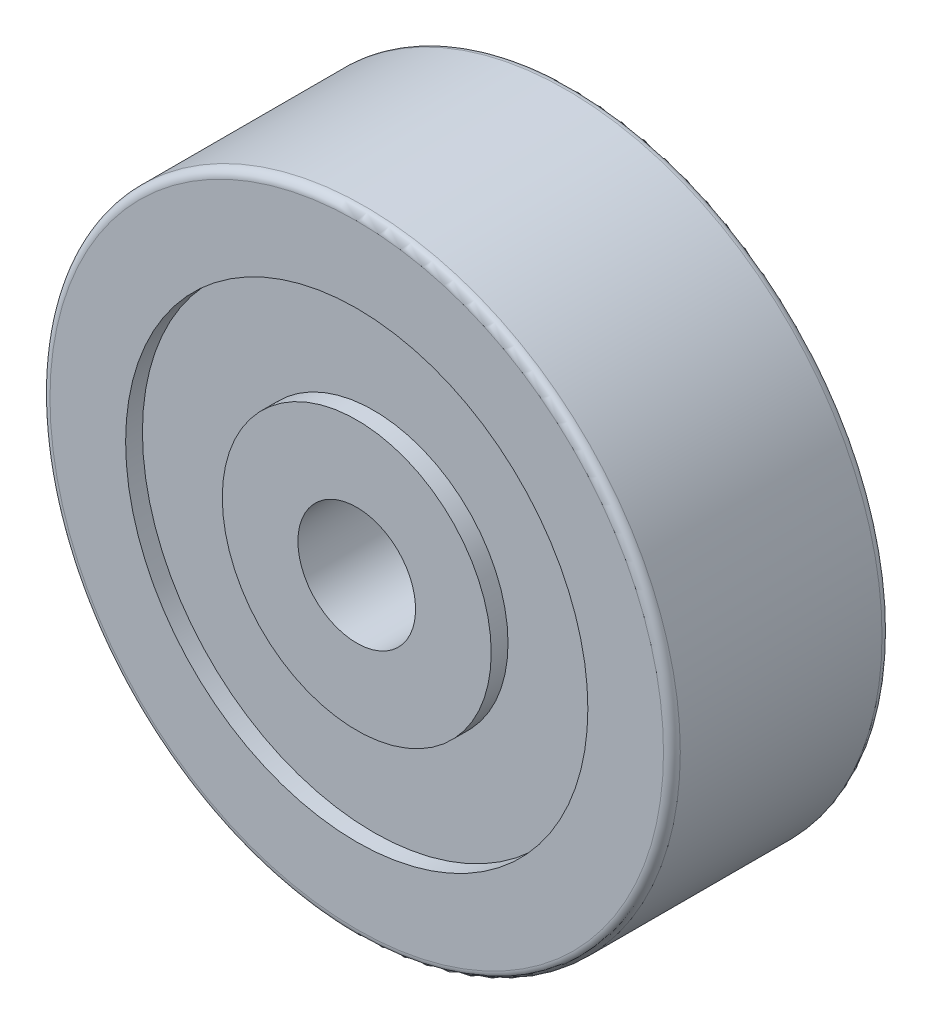
SolidWorks part; units mm, degrees
material "Alloy Steel"
ref_plane "Front Plane" through (0, 0, 0) normal (0, 0, 1) x (1, 0, 0)
ref_plane "Top Plane" through (0, 0, 0) normal (0, 1, 0) x (1, 0, 0)
ref_plane "Right Plane" through (0, 0, 0) normal (1, 0, 0) x (0, 0, -1)
sketch "Sketch1" plane through (0, 0, 0) normal (0, 0, 1) x (1, 0, 0)
  circle A0 centre (0, 0) radius 37.5
  dimension "D1" = 75
extrude "Boss-Extrude1" add sketch "Sketch1" against normal mid plane 26
ref_plane "Plane1" through (0, 0, 11) normal (0, 0, 1) x (1, 0, 0)
sketch "Sketch4" plane through (0, 0, -13) normal (0, 0, -1) x (-1, 0, 0)
  circle A0 centre (0, 0) radius 27.5
  dimension "D1" = 55
extrude "Cut-Extrude1" cut sketch "Sketch4" against normal blind 2
mirror "Mirror1" about plane through (0, 0, 0) normal (0, 0, 1) of "Cut-Extrude1"
sketch "Sketch5" plane through (0, 0, -11) normal (0, 0, -1) x (-1, 0, 0)
  circle A0 centre (0, 0) radius 16
  dimension "D1" = 32
extrude "Boss-Extrude2" add sketch "Sketch5" along normal blind 2
mirror "Mirror2" about plane through (0, 0, 0) normal (0, 0, 1) of "Boss-Extrude2"
sketch "Sketch6" plane through (0, 0, -13) normal (0, 0, -1) x (-1, 0, 0)
  circle A0 centre (0, 0) radius 7
  dimension "D1" = 14
extrude "Cut-Extrude2" cut sketch "Sketch6" against normal through all
fillet "Fillet1" radius 1 4 edges at (-27.5, 0, -13) (37.5, 0, 13) (37.5, 0, -13) (-16, 0, -13)
